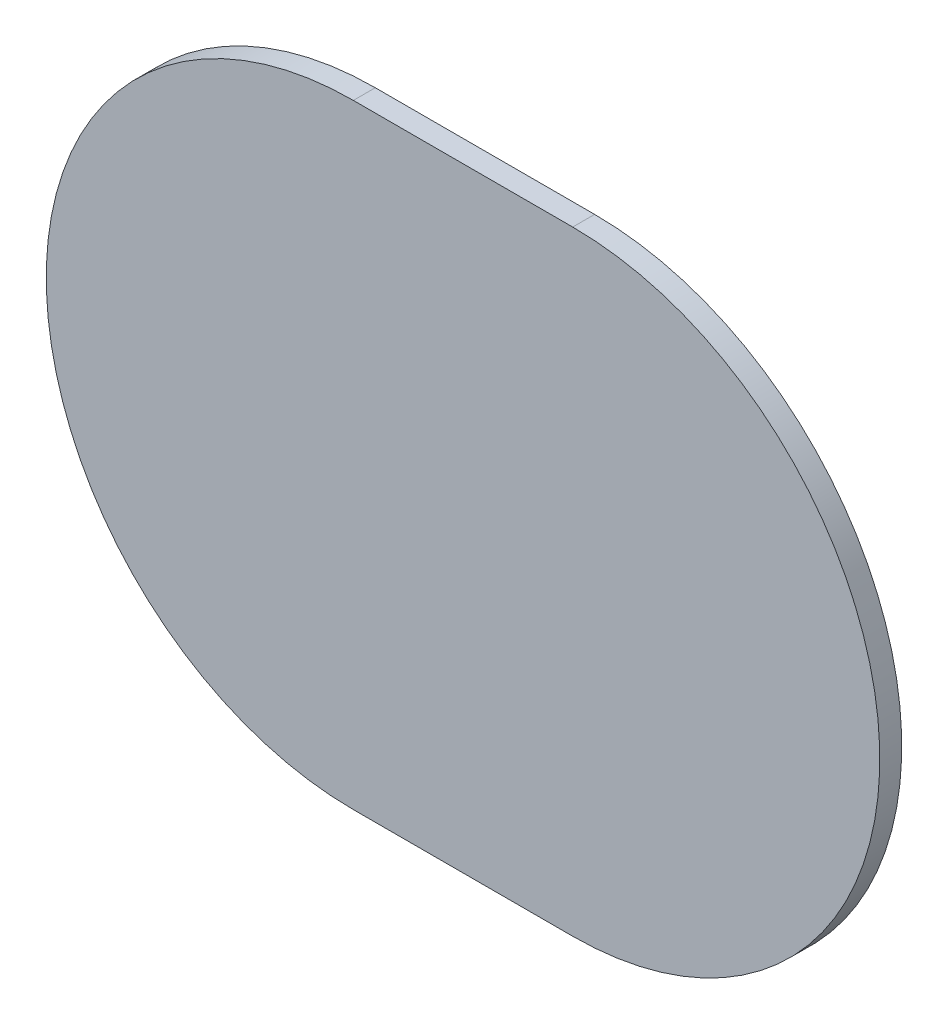
SolidWorks part; units mm, degrees
ref_plane "前视基准面" through (0, 0, 0) normal (0, 0, 1) x (1, 0, 0)
ref_plane "上视基准面" through (0, 0, 0) normal (0, 1, 0) x (1, 0, 0)
ref_plane "右视基准面" through (0, 0, 0) normal (1, 0, 0) x (0, 0, -1)
sketch "草图1" plane through (0, 0, 0) normal (0, 0, 1) x (1, 0, 0)
  line L0 (-20, 28) -> (0, 28) construction
  line L1 (0, -28) -> (-20, -28) construction
  line L2 (-20, 28) -> (0, 28)
  line L3 (0, -28) -> (-20, -28)
  arc A0 (-20, 28) -> (-20, -28) centre (-20, 0) ccw construction
  arc A1 (0, -28) -> (0, 28) centre (0, 0) ccw construction
  arc A2 (-20, 28) -> (-20, -28) centre (-20, 0) ccw
  arc A3 (0, -28) -> (0, 28) centre (0, 0) ccw
extrude "凸台-拉伸1" add sketch "草图1" along normal blind 2
